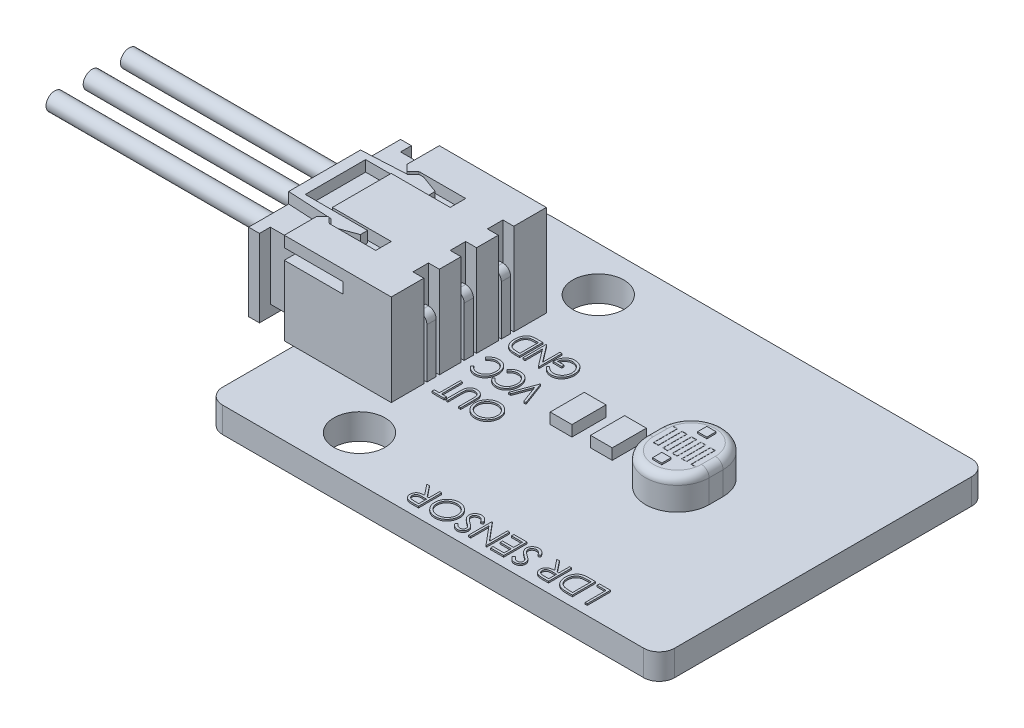
SolidWorks part; units mm, degrees
ref_plane "Front Plane" through (0, 0, 0) normal (0, 0, 1) x (1, 0, 0)
ref_plane "Top Plane" through (0, 0, 0) normal (0, 1, 0) x (1, 0, 0)
ref_plane "Right Plane" through (0, 0, 0) normal (1, 0, 0) x (0, 0, -1)
sketch "Sketch1" plane through (0, 0, 0) normal (0, 1, 0) x (1, 0, 0)
  line L0 (0, 10.575) -> (0, 0) construction
  line L1 (-14.575, 10.575) -> (14.575, 10.575)
  line L2 (-14.575, 10.575) -> (-14.575, -10.575)
  line L3 (-14.575, -10.575) -> (14.575, -10.575)
  line L4 (14.575, 10.575) -> (14.575, -10.575)
  line L5 (0, 0) -> (14.575, 0) construction
  dimension "D1" = 21.15
  dimension "D2" = 29.15
extrude "Boss-Extrude1" add sketch "Sketch1" along normal mid plane 1.65
sketch "Sketch2" plane through (0, 0.825, 0) normal (0, 1, 0) x (1, 0, 0)
  line L0 (-7.625, 7.7) -> (-7.625, -7.7) construction
  line L1 (-7.625, 0) -> (0, 0) construction
  line L3 (-14.575, 10.575) -> (-14.575, -10.575) construction
  circle A0 centre (-7.625, 7.7) radius 1.65
  circle A1 centre (-7.625, -7.7) radius 1.65
  dimension "D2" = 3.3
  dimension "D3" = 5.3
  dimension "D1" = 15.4
extrude "Cut-Extrude1" cut sketch "Sketch2" against normal through all
sketch "Sketch3" plane through (0, 0.825, 0) normal (0, 1, 0) x (1, 0, 0)
  line L0 (-14.575, 10.575) -> (-14.575, -10.575) construction
  line L1 (-8.275, 5) -> (-15.175, 5)
  line L2 (-8.275, 5) -> (-8.275, -5)
  line L3 (-8.275, -5) -> (-15.175, -5)
  line L4 (-15.175, 5) -> (-15.175, -5)
  line L5 (-8.275, 0) -> (-14.575, 0) construction
  dimension "D1" = 10
  dimension "D2" = 6.9
  dimension "D3" = 6.3
extrude "Boss-Extrude2" add sketch "Sketch3" along normal blind 5.9
sketch "Sketch4" plane through (-15.175, 0, 0) normal (-1, 0, 0) x (0, 0, 1)
  line L0 (-4.3, 6.025) -> (-4.3, 1.525)
  line L1 (-4.3, 1.525) -> (4.3, 1.525)
  line L2 (4.3, 1.525) -> (4.3, 6.025)
  line L3 (4.3, 6.025) -> (-4.3, 6.025)
  line L4 (-5, 0.825) -> (5, 0.825)
  line L5 (5, 0.825) -> (5, 6.725)
  line L6 (5, 6.725) -> (-5, 6.725)
  line L7 (-5, 6.725) -> (-5, 0.825)
  line L8 (-5, 0.825) -> (5, 0.825)
  line L9 (5, 0.825) -> (5, 6.725)
  line L10 (5, 6.725) -> (-5, 6.725)
  line L11 (-5, 6.725) -> (-5, 0.825)
  dimension "D1" = 0
  dimension "D2" = 0.7
extrude "Cut-Extrude2" cut sketch "Sketch4" against normal offset from surface (5.9 mm away) 1 contours L2 L3 L0 L1 up to face at (-8.275, 3.775, 0)
sketch "Sketch5" plane through (-15.175, 0, 0) normal (-1, 0, 0) x (0, 0, 1)
  line L0 (-5, 6.725) -> (-5, 0.825) construction
  line L1 (-5, 6.025) -> (-2.9, 6.025)
  line L2 (-5, 6.025) -> (-5, 5.325)
  line L3 (-5, 5.325) -> (5, 5.325)
  line L4 (5, 6.025) -> (5, 5.325)
  line L5 (5, 6.725) -> (5, 0.825) construction
  line L6 (0, -0.825) -> (0, 6.725) construction
  line L7 (-10.575, -0.825) -> (10.575, -0.825) construction
  line L8 (-5, 6.725) -> (5, 6.725) construction
  line L9 (-2.4, 6.725) -> (-2.4, -0.825) construction
  line L10 (2.4, 6.725) -> (2.4, -0.825) construction
  line L12 (-2.9, 6.725) -> (-1.9, 6.725)
  line L13 (-2.9, 6.725) -> (-2.9, 6.025)
  line L15 (-1.9, 6.725) -> (-1.9, 6.025)
  line L16 (1.9, 6.725) -> (1.9, 6.025)
  line L17 (2.9, 6.725) -> (1.9, 6.725)
  line L18 (2.9, 6.725) -> (2.9, 6.025)
  line L19 (4.3, 6.025) -> (-4.3, 6.025) construction
  line L20 (-1.9, 6.025) -> (1.9, 6.025)
  line L21 (2.9, 6.025) -> (5, 6.025)
  dimension "D1" = 2.4
  dimension "D2" = 1
  dimension "D3" = 0.7
extrude "Cut-Extrude3" cut sketch "Sketch5" against normal blind 3.8
sketch "Sketch6" plane through (0, 6.725, 0) normal (0, 1, 0) x (1, 0, 0)
  line L0 (-8.275, -5) -> (-8.275, 5) construction
  line L1 (-8.275, 2.9) -> (-8.975, 2.9)
  line L2 (-8.275, 2.9) -> (-8.275, 1.9)
  line L3 (-8.275, 1.9) -> (-8.975, 1.9)
  line L4 (-8.975, 2.9) -> (-8.975, 1.9)
  line L5 (-11.375, -2.9) -> (-15.175, -2.9) construction
  line L6 (-8.275, 0.5) -> (-8.975, 0.5)
  line L7 (-8.275, 0.5) -> (-8.275, -0.5)
  line L8 (-8.275, -0.5) -> (-8.975, -0.5)
  line L9 (-8.975, 0.5) -> (-8.975, -0.5)
  line L10 (-8.275, -1.9) -> (-8.975, -1.9)
  line L11 (-8.275, -1.9) -> (-8.275, -2.9)
  line L12 (-8.275, -2.9) -> (-8.975, -2.9)
  line L13 (-8.975, -1.9) -> (-8.975, -2.9)
  line L14 (-11.375, -2.9) -> (-11.375, -1.9) construction
  line L15 (-11.375, 2.9) -> (-15.175, 2.9) construction
  point P16 (-8.625, -2.9)
  point P21 (-8.275, 0)
  dimension "D1" = 0.7
extrude "Cut-Extrude4" cut sketch "Sketch6" against normal up to surface (5.9 mm away) up to face at (-5.7125, 0.825, 0)
sketch "Sketch7" plane through (0, 0.825, 0) normal (0, 1, 0) x (1, 0, 0)
  line L0 (-8.875, 2.4) -> (-8.975, 2.4) construction
  line L1 (-8.875, 2.7) -> (-8.275, 2.7)
  line L2 (-8.875, 2.7) -> (-8.875, 2.1)
  line L3 (-8.875, 2.1) -> (-8.275, 2.1)
  line L4 (-8.275, 2.7) -> (-8.275, 2.1)
  line L5 (-8.975, 1.9) -> (-8.975, 2.9) construction
  line L6 (-8.275, 2.9) -> (-8.275, 5) construction
  line L7 (-8.275, 1.2) -> (-8.975, 1.2) construction
  line L8 (-8.275, 0.5) -> (-8.275, 1.9) construction
  line L9 (-8.975, 1.2) -> (-8.975, 0) construction
  line L10 (-8.975, 0.5) -> (-8.975, -0.5) construction
  line L11 (-8.975, 0) -> (-8.275, 0) construction
  line L12 (-8.875, 0) -> (-8.975, 0) construction
  line L13 (-8.275, -0.3) -> (-8.275, 0.3)
  line L14 (-8.875, 0.3) -> (-8.275, 0.3)
  line L15 (-8.875, -0.3) -> (-8.875, 0.3)
  line L16 (-8.875, -0.3) -> (-8.275, -0.3)
  line L17 (-8.875, 2.7) -> (-8.275, 2.7)
  line L18 (-8.875, 2.1) -> (-8.275, 2.1)
  line L19 (-8.875, -2.4) -> (-8.975, -2.4) construction
  line L20 (-8.875, -2.1) -> (-8.275, -2.1)
  line L21 (-8.875, -2.7) -> (-8.275, -2.7)
  line L22 (-8.275, -2.7) -> (-8.275, -2.1)
  line L23 (-8.875, -2.1) -> (-8.275, -2.1)
  line L24 (-8.875, -2.7) -> (-8.875, -2.1)
  line L25 (-8.875, -2.7) -> (-8.275, -2.7)
  dimension "D1" = 0.6
extrude "Boss-Extrude3" add sketch "Sketch7" along normal blind 3.7 and the other way offset from surface (2.65 mm away) 1 contours L24 L21 L22 L20 | L15 L16 L13 L14 | L4 L1 L2 L3 other way up to face at (-7.625, -0.825, -6.05)
sketch "Sketch8" plane through (-8.275, 0, 0) normal (1, 0, 0) x (0, 0, -1)
  line L0 (-2.1, 4.525) -> (-2.1, 0.825) construction
  line L1 (-2.7, 4.525) -> (-2.1, 4.525)
  line L2 (-2.7, 4.525) -> (-2.7, 3.925)
  line L3 (-2.7, 3.925) -> (-2.1, 3.925)
  line L4 (-2.1, 4.525) -> (-2.1, 3.925)
  line L5 (0.3, 4.525) -> (0.3, 0.825) construction
  line L6 (-0.3, 4.525) -> (0.3, 4.525)
  line L7 (-0.3, 4.525) -> (-0.3, 3.925)
  line L8 (-0.3, 3.925) -> (0.3, 3.925)
  line L9 (0.3, 4.525) -> (0.3, 3.925)
  line L10 (2.7, 4.525) -> (2.7, 0.825) construction
  line L11 (2.1, 4.525) -> (2.7, 4.525)
  line L12 (2.1, 4.525) -> (2.1, 3.925)
  line L13 (2.1, 3.925) -> (2.7, 3.925)
  line L14 (2.7, 4.525) -> (2.7, 3.925)
extrude "Boss-Extrude4" add sketch "Sketch8" against normal offset from surface (6.4 mm away) 0.5 up to face at (-15.175, 3.25, 0)
sketch "Sketch9" plane through (0, 6.725, 0) normal (0, 1, 0) x (1, 0, 0)
  line L0 (-15.175, 0) -> (-13.2998, 0) construction
  line L1 (-15.175, 1.9) -> (-15.175, -1.9) construction
  line L2 (-15.175, 2.9) -> (-14.775, 2.5)
  line L4 (-14.775, 2.5) -> (-14.375, 2.9)
  line L5 (-11.375, 2.9) -> (-15.175, 2.9) construction
  line L6 (-14.375, 2.9) -> (-15.175, 2.9)
  line L7 (-14.775, 2.9) -> (-14.775, 2.5) construction
  line L8 (-14.775, -2.9) -> (-14.775, -2.5) construction
  line L9 (-14.375, -2.9) -> (-15.175, -2.9)
  line L10 (-14.775, -2.5) -> (-14.375, -2.9)
  line L11 (-15.175, -2.9) -> (-14.775, -2.5)
  dimension "D1" = 0.4
  dimension "D2" = 0.8
extrude "Boss-Extrude5" add sketch "Sketch9" against normal up to surface (0.7 mm away) up to face at (-12.5375, 6.025, 0)
fillet "Fillet1" radius 0.5 3 edges at (-8.275, 4.525, -2.4) (-8.275, 4.525, 0) (-8.275, 4.525, 2.4)
chamfer "Chamfer1" distance 0.25 angle 45 24 edges at (-8.875, -1.825, 2.4) (-8.575, -1.825, 2.7) (-8.275, -1.825, 2.4) (-8.575, -1.825, 2.1) (-8.875, -1.825, 0) (-8.575, -1.825, 0.3) (-8.275, -1.825, 0) (-8.575, -1.825, -0.3) (-8.275, -1.825, -2.4) (-8.575, -1.825, -2.7) (-8.875, -1.825, -2.4) (-8.575, -1.825, -2.1) (-14.675, 3.925, 2.4) (-14.675, 4.225, 2.1) (-14.675, 4.525, 2.4) (-14.675, 4.225, 2.7) (-14.675, 3.925, 0) (-14.675, 4.225, -0.3) (-14.675, 4.525, 0) (-14.675, 4.225, 0.3) (-14.675, 3.925, -2.4) (-14.675, 4.225, -2.7) (-14.675, 4.525, -2.4) (-14.675, 4.225, -2.1)
fillet "Fillet2" radius 0.1 6 edges at (-14.375, 6.375, 2.9) (-14.775, 6.375, 2.5) (-15.175, 6.375, 2.9) (-14.775, 6.375, -2.5) (-14.375, 6.375, -2.9) (-15.175, 6.375, -2.9)
fillet "Fillet3" radius 1 4 edges at (-14.575, 0, -10.575) (-14.575, 0, 10.575) (14.575, 0, -10.575) (14.575, 0, 10.575)
sketch "Sketch10" plane through (0, 0.825, 0) normal (0, 1, 0) x (1, 0, 0)
  line L0 (5.625, 0.45) -> (5.625, -0.45) construction
  line L1 (7.675, 0.45) -> (7.675, -0.45)
  line L2 (3.575, 0.45) -> (3.575, -0.45)
  line L3 (5.625, 0) -> (0, 0) construction
  line L4 (14.575, -9.575) -> (14.575, 9.575) construction
  arc A0 (7.675, 0.45) -> (3.575, 0.45) centre (5.625, 0.45) ccw
  arc A1 (3.575, -0.45) -> (7.675, -0.45) centre (5.625, -0.45) ccw
  point P2 (5.625, 0)
  dimension "D2" = 5
  dimension "D1" = 4.1
  dimension "D3" = 11
extrude "Boss-Extrude6" add sketch "Sketch10" along normal blind 2
fillet "Fillet4" radius 0.5 4 edges at (3.575, 2.825, 0) (5.625, 2.825, -2.5) (7.675, 2.825, 0) (5.625, 2.825, 2.5)
sketch "Sketch11" plane through (0, 2.825, 0) normal (0, 1, 0) x (1, 0, 0)
  line L0 (5.625, 1.15) -> (5.625, -1.15) construction
  line L1 (5.325, 1.75) -> (5.925, 1.75)
  line L2 (5.325, 1.75) -> (5.325, 1.15)
  line L3 (5.325, 1.15) -> (5.925, 1.15)
  line L4 (5.925, 1.75) -> (5.925, 1.15)
  line L5 (5.325, -1.15) -> (5.925, -1.15)
  line L6 (5.325, -1.15) -> (5.325, -1.75)
  line L7 (5.325, -1.75) -> (5.925, -1.75)
  line L8 (5.925, -1.15) -> (5.925, -1.75)
  line L9 (5.625, -1.15) -> (5.625, -2) construction
  line L10 (5.625, 0) -> (4.075, 0) construction
  line L11 (4.075, 0.45) -> (4.075, -0.45) construction
  arc A0 (4.075, -0.45) -> (7.175, -0.45) centre (5.625, -0.45) ccw construction
  dimension "D1" = 0.6
  dimension "D2" = 3.5
extrude "Boss-Extrude7" add sketch "Sketch11" along normal blind 0.1 and the other way offset from surface (4.65 mm away) 1 other way up to face at (-8.575, -0.825, 0)
sketch "Sketch12" plane through (0, 0.825, 0) normal (0, 1, 0) x (1, 0, 0)
  line L0 (0.675, 0) -> (0, 0) construction
  line L1 (0.675, 1.1) -> (2.075, 1.1)
  line L2 (0.675, 1.1) -> (0.675, -1.1)
  line L3 (0.675, -1.1) -> (2.075, -1.1)
  line L4 (2.075, 1.1) -> (2.075, -1.1)
  line L5 (-0.525, 1.1) -> (-1.925, 1.1)
  line L6 (-0.525, 1.1) -> (-0.525, -1.1)
  line L7 (-0.525, -1.1) -> (-1.925, -1.1)
  line L8 (-1.925, 1.1) -> (-1.925, -1.1)
  line L9 (0, 0) -> (-0.525, 0) construction
  line L10 (7.675, -0.45) -> (7.675, 0.45) construction
  dimension "D1" = 1.4
  dimension "D2" = 2.2
  dimension "D3" = 4
  dimension "D4" = 9.6
extrude "Boss-Extrude8" add sketch "Sketch12" along normal blind 0.7
sketch "Sketch13" plane through (0, 0.825, 0) normal (0, 1, 0) x (1, 0, 0)
  line L0 (-8.275, 0.75) -> (-3.775, 0.75) construction
  line L1 (-8.275, 0.5) -> (-8.275, 1.9) construction
  line L2 (-8.275, -1.65) -> (-3.775, -1.65) construction
  line L3 (-8.275, -1.9) -> (-8.275, -0.5) construction
  line L4 (-8.275, 3.15) -> (-3.775, 3.15) construction
  line L5 (-8.275, 2.9) -> (-8.275, 5) construction
  line L6 (10.5308, -8.5099) -> (-3.5536, -8.5099) construction
  line L7 (-8.275, -2.4) -> (-8.275, -1.65) construction
  line L8 (-8.275, -2.7) -> (-8.275, -2.1) construction
  line L9 (-8.275, 0) -> (-8.275, 0.75) construction
  line L10 (-8.275, -0.3) -> (-8.275, 0.3) construction
  line L11 (-8.275, 2.4) -> (-8.275, 3.15) construction
  line L12 (-8.275, 2.7) -> (-8.275, 2.1) construction
  text T0 "OUT" font "Century Gothic" height 1.5
  text T1 "VCC" font "Century Gothic" height 1.5
  text T2 "GND" font "Century Gothic" height 1.5
  text T3 "LDR SENSOR" font "Century Gothic" height 1.5
  dimension "D1" = 0.75
  dimension "D2" = 4.5
extrude "Boss-Extrude9" add sketch "Sketch13" along normal blind 0.1
sketch "Sketch14" plane through (0, 2.825, 0) normal (0, 1, 0) x (1, 0, 0)
  line L0 (7.1419, -0.7686) -> (6.8385, -0.7686) construction
  line L1 (6.8385, -0.7686) -> (6.8385, 0.7686) construction
  line L2 (6.8385, 0.7686) -> (6.5351, 0.7686) construction
  line L3 (6.5351, 0.7686) -> (6.5351, -0.7686) construction
  line L4 (6.5351, -0.7686) -> (6.2318, -0.7686) construction
  line L5 (6.2318, -0.7686) -> (6.2318, 0.7686) construction
  line L6 (6.2318, 0.7686) -> (5.9284, 0.7686) construction
  line L7 (5.9284, 0.7686) -> (5.9284, -0.7686) construction
  line L8 (5.9284, -0.7686) -> (5.625, -0.7686) construction
  line L9 (5.625, -0.7686) -> (5.625, 0.7686) construction
  line L10 (5.625, 0.7686) -> (5.3216, 0.7686) construction
  line L11 (5.3216, 0.7686) -> (5.3216, -0.7686) construction
  line L12 (5.3216, -0.7686) -> (5.0182, -0.7686) construction
  line L13 (5.0182, -0.7686) -> (5.0182, 0.7686) construction
  line L14 (5.0182, 0.7686) -> (4.7149, 0.7686) construction
  line L15 (4.7149, 0.7686) -> (4.7149, -0.7686) construction
  line L16 (4.7149, -0.7686) -> (4.4115, -0.7686) construction
  line L17 (4.4115, -0.7686) -> (4.4115, 0.7686) construction
  line L18 (4.4115, 0.7686) -> (4.1081, 0.7686) construction
  line L19 (5.625, 0) -> (7.175, 0) construction
  line L20 (7.175, -0.45) -> (7.175, 0.45) construction
  line L21 (7.144, -0.7586) -> (6.8485, -0.7586)
  line L22 (6.8485, -0.7586) -> (6.8485, 0.7786)
  line L23 (6.8485, 0.7786) -> (6.5251, 0.7786)
  line L24 (6.5251, 0.7786) -> (6.5251, -0.7586)
  line L25 (6.5251, -0.7586) -> (6.2418, -0.7586)
  line L26 (6.2418, -0.7586) -> (6.2418, 0.7786)
  line L27 (6.2418, 0.7786) -> (5.9184, 0.7786)
  line L28 (5.9184, 0.7786) -> (5.9184, -0.7586)
  line L29 (5.9184, -0.7586) -> (5.635, -0.7586)
  line L30 (5.635, -0.7586) -> (5.635, 0.7786)
  line L31 (5.635, 0.7786) -> (5.3116, 0.7786)
  line L32 (5.3116, 0.7786) -> (5.3116, -0.7586)
  line L33 (5.3116, -0.7586) -> (5.0282, -0.7586)
  line L34 (5.0282, -0.7586) -> (5.0282, 0.7786)
  line L35 (5.0282, 0.7786) -> (4.7049, 0.7786)
  line L36 (4.7049, 0.7786) -> (4.7049, -0.7586)
  line L37 (4.7049, -0.7586) -> (4.4215, -0.7586)
  line L38 (4.4215, -0.7586) -> (4.4215, 0.7786)
  line L39 (4.4215, 0.7786) -> (4.1102, 0.7786)
  line L40 (7.1398, -0.7786) -> (6.8285, -0.7786)
  line L41 (6.8285, -0.7786) -> (6.8285, 0.7586)
  line L42 (6.8285, 0.7586) -> (6.5451, 0.7586)
  line L43 (6.5451, 0.7586) -> (6.5451, -0.7786)
  line L44 (6.5451, -0.7786) -> (6.2218, -0.7786)
  line L45 (6.2218, -0.7786) -> (6.2218, 0.7586)
  line L46 (6.2218, 0.7586) -> (5.9384, 0.7586)
  line L47 (5.9384, 0.7586) -> (5.9384, -0.7786)
  line L48 (5.9384, -0.7786) -> (5.615, -0.7786)
  line L49 (5.615, -0.7786) -> (5.615, 0.7586)
  line L50 (5.615, 0.7586) -> (5.3316, 0.7586)
  line L51 (5.3316, 0.7586) -> (5.3316, -0.7786)
  line L52 (5.3316, -0.7786) -> (5.0082, -0.7786)
  line L53 (5.0082, -0.7786) -> (5.0082, 0.7586)
  line L54 (5.0082, 0.7586) -> (4.7249, 0.7586)
  line L55 (4.7249, 0.7586) -> (4.7249, -0.7786)
  line L56 (4.7249, -0.7786) -> (4.4015, -0.7786)
  line L57 (4.4015, -0.7786) -> (4.4015, 0.7586)
  line L58 (4.4015, 0.7586) -> (4.106, 0.7586)
  line L59 (4.4015, 0.7586) -> (4.1081, 0.7586) construction
  line L60 (4.4215, 0.7786) -> (4.1081, 0.7786) construction
  line L61 (7.1419, -0.7586) -> (6.8485, -0.7586) construction
  line L62 (7.1419, -0.7786) -> (6.8285, -0.7786) construction
  arc A0 (4.075, -0.45) -> (7.175, -0.45) centre (5.625, -0.45) ccw construction
  arc A1 (7.175, 0.45) -> (4.075, 0.45) centre (5.625, 0.45) ccw construction
  arc A2 (7.1398, -0.7786) -> (7.144, -0.7586) centre (5.625, -0.45) ccw
  arc A3 (4.1102, 0.7786) -> (4.106, 0.7586) centre (5.625, 0.45) ccw
  dimension "D1" = 0.01
  dimension "D2" = 0.01
extrude "Boss-Extrude10" add sketch "Sketch14" along normal blind 0.01
sketch "Sketch15" plane through (-9.275, 0, 0) normal (-1, 0, 0) x (0, 0, 1)
  line L0 (4.2, 5.925) -> (-4.2, 5.925)
  line L1 (-4.2, 5.925) -> (-4.2, 1.625)
  line L2 (-4.2, 1.625) -> (4.2, 1.625)
  line L3 (4.2, 1.625) -> (4.2, 5.925)
  line L4 (4.3, 1.525) -> (4.3, 6.025)
  line L5 (4.3, 6.025) -> (-4.3, 6.025)
  line L6 (-4.3, 6.025) -> (-4.3, 1.525)
  line L7 (-4.3, 1.525) -> (4.3, 1.525)
  line L8 (4.3, 1.525) -> (4.3, 6.025) construction
  line L9 (4.3, 6.025) -> (-4.3, 6.025) construction
  line L10 (-4.3, 6.025) -> (-4.3, 1.525) construction
  line L11 (-4.3, 1.525) -> (4.3, 1.525) construction
  line L12 (2.1, 3.925) -> (2.7, 3.925) construction
  line L13 (2.7, 4.525) -> (2.7, 3.925) construction
  line L14 (2.7, 4.525) -> (2.1, 4.525) construction
  line L15 (2.1, 3.925) -> (2.1, 4.525) construction
  line L16 (0.3, 3.925) -> (-0.3, 3.925) construction
  line L17 (0.3, 4.525) -> (0.3, 3.925) construction
  line L18 (-0.3, 4.525) -> (0.3, 4.525) construction
  line L19 (-0.3, 3.925) -> (-0.3, 4.525) construction
  line L20 (-2.1, 4.525) -> (-2.1, 3.925) construction
  line L21 (-2.7, 4.525) -> (-2.1, 4.525) construction
  line L22 (-2.7, 3.925) -> (-2.7, 4.525) construction
  line L23 (-2.1, 3.925) -> (-2.7, 3.925) construction
  line L24 (2.1, 3.925) -> (2.7, 3.925) construction
  line L25 (2.7, 4.525) -> (2.7, 3.925) construction
  line L26 (2.7, 4.525) -> (2.1, 4.525) construction
  line L27 (2.1, 3.925) -> (2.1, 4.525) construction
  line L28 (0.3, 3.925) -> (-0.3, 3.925) construction
  line L29 (0.3, 4.525) -> (0.3, 3.925) construction
  line L30 (-0.3, 4.525) -> (0.3, 4.525) construction
  line L31 (-0.3, 3.925) -> (-0.3, 4.525) construction
  line L32 (-2.1, 4.525) -> (-2.1, 3.925) construction
  line L33 (-2.7, 4.525) -> (-2.1, 4.525) construction
  line L34 (-2.7, 3.925) -> (-2.7, 4.525) construction
  line L35 (-2.1, 3.925) -> (-2.7, 3.925) construction
  line L36 (2, 3.825) -> (2.8, 3.825)
  line L37 (2.8, 4.625) -> (2.8, 3.825)
  line L38 (2.8, 4.625) -> (2, 4.625)
  line L39 (2, 3.825) -> (2, 4.625)
  line L40 (0.4, 3.825) -> (-0.4, 3.825)
  line L41 (-0.4, 3.825) -> (-0.4, 4.625)
  line L42 (-0.4, 4.625) -> (0.4, 4.625)
  line L43 (0.4, 4.625) -> (0.4, 3.825)
  line L44 (-2, 3.825) -> (-2.8, 3.825)
  line L45 (-2.8, 3.825) -> (-2.8, 4.625)
  line L46 (-2.8, 4.625) -> (-2, 4.625)
  line L47 (-2, 4.625) -> (-2, 3.825)
  dimension "D1" = 0
  dimension "D2" = 0.1
  dimension "D3" = 0.1
extrude "Boss-Extrude11" add sketch "Sketch15" along normal offset from surface (6.6 mm away) 1.7 from offset 1 up to face at (-15.175, 6.375, 0) offset beyond the face yes
sketch "Sketch16" plane through (-16.875, 0, 0) normal (-1, 0, 0) x (0, 0, 1)
  line L0 (-4.9, 6.625) -> (-4.9, 0.925)
  line L1 (-4.9, 0.925) -> (4.9, 0.925)
  line L2 (4.9, 0.925) -> (4.9, 6.625)
  line L3 (4.9, 6.625) -> (-4.9, 6.625)
  line L4 (4.2, 5.925) -> (-4.2, 5.925)
  line L5 (-4.2, 5.925) -> (-4.2, 1.625)
  line L6 (-4.2, 1.625) -> (4.2, 1.625)
  line L7 (4.2, 1.625) -> (4.2, 5.925)
  line L8 (4.2, 5.925) -> (-4.2, 5.925) construction
  line L9 (-4.2, 5.925) -> (-4.2, 1.625) construction
  line L10 (-4.2, 1.625) -> (4.2, 1.625) construction
  line L11 (4.2, 1.625) -> (4.2, 5.925) construction
  dimension "D1" = 0
  dimension "D2" = 0.7
extrude "Boss-Extrude12" add sketch "Sketch16" along normal blind 0.7
sketch "Sketch17" plane through (0, 5.925, 0) normal (0, 1, 0) x (1, 0, 0)
  line L0 (-14.324, 2.8388) -> (-14.6934, 2.4695)
  line L1 (-14.6934, 2.4695) -> (-16.875, 2.354)
  line L2 (-16.875, -4.9) -> (-16.875, 4.9) construction
  line L3 (-16.875, 2.354) -> (-16.875, 1.946)
  line L4 (-16.875, 1.946) -> (-12.8534, 1.946)
  line L5 (-12.8534, 1.946) -> (-12.8534, 2.4117)
  line L6 (-12.8534, 2.4117) -> (-14.0231, 2.8388)
  line L7 (-14.0231, 2.8388) -> (-14.324, 2.8388)
  line L8 (-16.875, 0) -> (-12.7302, 0) construction
  line L9 (-14.7043, 2.5707) -> (-14.4043, 2.8707) construction
  line L10 (-14.0231, -2.8388) -> (-14.324, -2.8388)
  line L11 (-12.8534, -2.4117) -> (-14.0231, -2.8388)
  line L12 (-12.8534, -1.946) -> (-12.8534, -2.4117)
  line L13 (-16.875, -1.946) -> (-12.8534, -1.946)
  line L14 (-16.875, -2.354) -> (-16.875, -1.946)
  line L15 (-14.6934, -2.4695) -> (-16.875, -2.354)
  line L16 (-14.324, -2.8388) -> (-14.6934, -2.4695)
  point P13 (-14.3142, 2.8388)
extrude "Boss-Extrude13" add sketch "Sketch17" along normal up to surface (0.7 mm away) up to face at (-17.225, 6.625, 0)
sketch "Sketch18" plane through (0, 6.625, 0) normal (0, 1, 0) x (1, 0, 0)
  line L0 (-16.875, 2.354) -> (-17.575, 2.3169)
  line L1 (-17.575, -4.9) -> (-17.575, 4.9) construction
  line L2 (-16.875, -2.354) -> (-17.575, -2.3169)
  line L3 (-14.6934, -2.4695) -> (-16.875, -2.354) construction
  line L4 (-14.6934, 2.4695) -> (-16.875, 2.354) construction
  line L5 (-17.575, -2.3169) -> (-17.575, -4.9)
  line L23 (-16.875, -4.9) -> (-16.875, -2.354)
  line L24 (-16.875, -2.354) -> (-14.6934, -2.4695)
  line L25 (-14.6934, -2.4695) -> (-14.324, -2.8388)
  line L26 (-14.324, -2.8388) -> (-14.0231, -2.8388)
  line L27 (-14.0231, -2.8388) -> (-12.8534, -2.4117)
  line L28 (-12.8534, -2.4117) -> (-12.8534, -1.946)
  line L29 (-12.8534, -1.946) -> (-16.875, -1.946)
  line L30 (-16.875, -1.946) -> (-16.875, 1.946)
  line L31 (-16.875, 1.946) -> (-12.8534, 1.946)
  line L32 (-12.8534, 1.946) -> (-12.8534, 2.4117)
  line L33 (-12.8534, 2.4117) -> (-14.0231, 2.8388)
  line L34 (-14.0231, 2.8388) -> (-14.324, 2.8388)
  line L35 (-14.324, 2.8388) -> (-14.6934, 2.4695)
  line L36 (-14.6934, 2.4695) -> (-16.875, 2.354)
  line L37 (-16.875, 2.354) -> (-16.875, 4.9)
  line L38 (-16.875, 4.9) -> (-17.575, 4.9)
  line L39 (-17.575, 4.9) -> (-17.575, -4.9)
  line L40 (-17.575, -4.9) -> (-16.875, -4.9)
  line L41 (-16.875, -4.9) -> (-16.875, -2.354)
  line L55 (-16.875, 2.354) -> (-16.875, 4.9)
  line L56 (-16.875, 4.9) -> (-17.575, 4.9)
  line L57 (-17.575, 4.9) -> (-17.575, 2.3169)
  line L58 (-17.575, -4.9) -> (-16.875, -4.9)
  dimension "D1" = 0
extrude "Cut-Extrude5" cut sketch "Sketch18" against normal up to surface (0.7 mm away) up to face at (-14.4052, 5.925, 0)
sketch "Sketch19" plane through (-17.575, 0, 0) normal (-1, 0, 0) x (0, 0, 1)
  line L0 (0, 0.925) -> (0, 4.739) construction
  line L1 (-4.9, 0.925) -> (4.9, 0.925) construction
  line L2 (-2.4, 4.225) -> (-2, 4.225) construction
  line L3 (-2, 4.625) -> (-2, 3.825) construction
  line L5 (-2.8, 4.625) -> (-2, 4.625) construction
  line L6 (-2.4, 4.625) -> (-2.4, 4.225) construction
  circle A0 centre (-2.4, 4.225) radius 0.5657
  circle A1 centre (2.4, 4.225) radius 0.5657
  circle A2 centre (0, 4.225) radius 0.5657
  point P18 (0, 0)
extrude "Boss-Extrude14" add sketch "Sketch19" along normal blind 15
